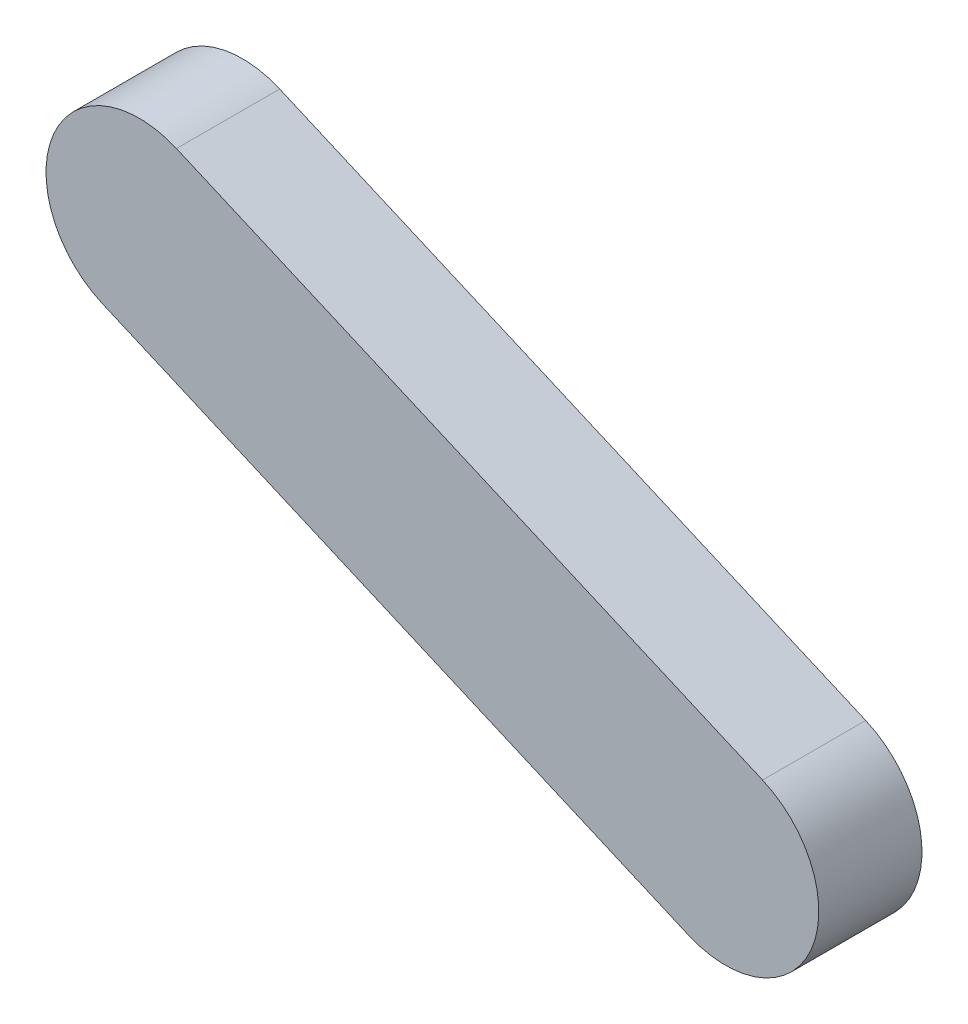
SolidWorks part; units mm, degrees
ref_plane "Front" through (0, 0, 0) normal (0, 0, 1) x (1, 0, 0)
ref_plane "Top" through (0, 0, 0) normal (0, 1, 0) x (1, 0, 0)
ref_plane "Right" through (0, 0, 0) normal (1, 0, 0) x (0, 0, -1)
sketch "Sketch1" plane through (0, 0, 0) normal (0, 0, 1) x (1, 0, 0)
  line L0 (-991.7389, 460.6206) -> (-1294.7381, 591.859) construction
  line L1 (-991.7389, 460.6206) -> (-1294.7381, 591.859)
  line L2 (-1275.5571, 636.1435) -> (-972.5579, 504.9051)
  line L3 (-1313.9191, 547.5745) -> (-1010.9199, 416.3361)
  arc A1 (-972.5579, 504.9051) -> (-1010.9199, 416.3361) centre (-991.7389, 460.6206) cw
  arc A2 (-999.9394, 508.1788) -> (-985.128, 412.8156) centre (-991.7389, 460.6206) ccw construction
  arc A3 (-1275.5571, 636.1435) -> (-1313.9191, 547.5745) centre (-1294.7381, 591.859) ccw
extrude "Boss-Extrude1" add sketch "Sketch1" along normal blind 53.34
equation "\"mass\"= \"human weight@FS2-FR-HA-A-0001-V1, HUMAN ANALOG.Assembly\" * \"forearm percent@FS2-FR-HA-A-0001-V1, HUMAN ANALOG.Assembly\" + \"human weight@FS2-FR-HA-A-0001-V1, HUMAN ANALOG.Assembly\" * \"hand percent@FS2-FR-HA-A-0001-V1, HUMAN ANALOG.Assembly\""
